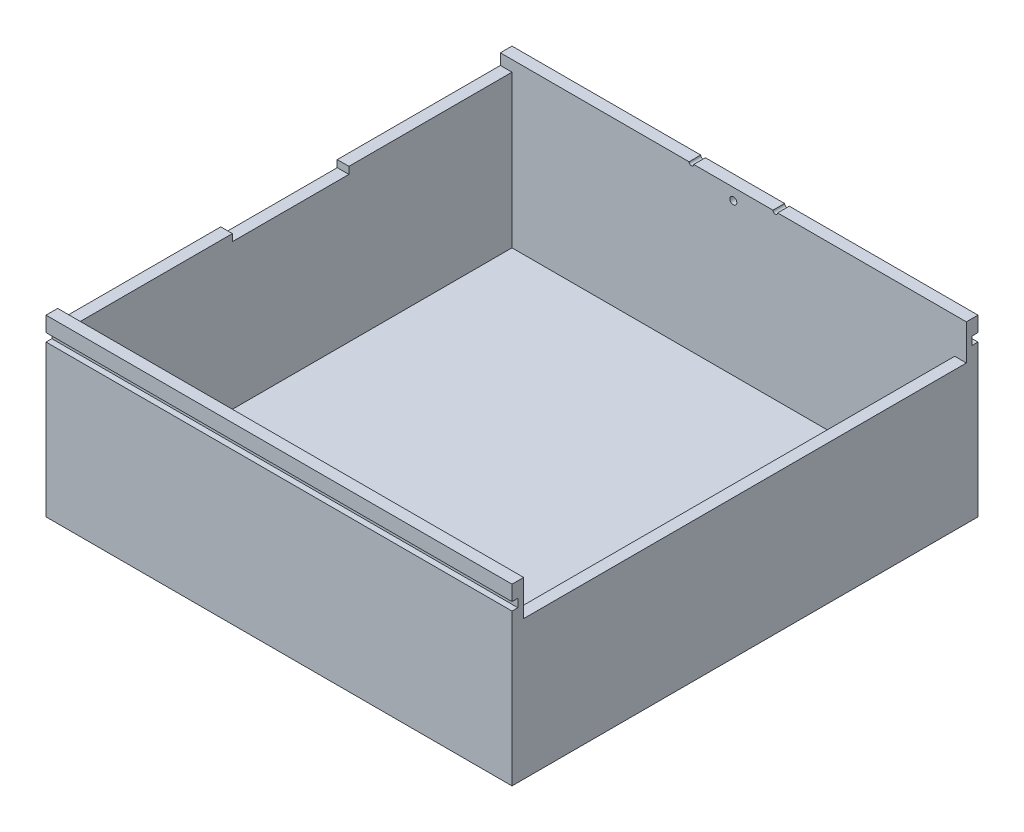
SolidWorks part; units mm, degrees
ref_plane "Спереди" through (0, 0, 0) normal (0, 0, 1) x (1, 0, 0)
ref_plane "Сверху" through (0, 0, 0) normal (0, 1, 0) x (1, 0, 0)
ref_plane "Справа" through (0, 0, 0) normal (1, 0, 0) x (0, 0, -1)
sketch "Эскиз1" plane through (0, 0, 0) normal (0, 1, 0) x (1, 0, 0)
  line L1 (100, -100) -> (-100, -100)
  line L2 (100, -100) -> (100, 100)
  line L3 (100, 100) -> (-100, 100)
  line L4 (-100, -100) -> (-100, 100)
  line L5 (100, -100) -> (-100, 100) construction
  line L6 (100, 100) -> (-100, -100) construction
  point P0 (0, 0)
  dimension "D1" = 200
  dimension "D2" = 200
extrude "Бобышка-Вытянуть2" add sketch "Эскиз1" along normal blind 5
sketch "Эскиз2" plane through (0, 5, 0) normal (0, 1, 0) x (1, 0, 0)
  line L0 (100, -100) -> (100, 100) construction
  line L1 (-100, -100) -> (100, -100)
  line L2 (-100, -100) -> (-100, -95)
  line L3 (-100, -95) -> (100, -95)
  line L4 (100, -100) -> (100, -95)
  point P7 (100, -97.5)
  dimension "D1" = 2.5
extrude "Бобышка-Вытянуть3" add sketch "Эскиз2" along normal blind 70
sketch "Эскиз3" plane through (0, 5, 0) normal (0, 1, 0) x (1, 0, 0)
  line L2 (100, -95) -> (95, -95)
  line L3 (100, -95) -> (100, 95)
  line L4 (100, 95) -> (95, 95)
  line L5 (95, -95) -> (95, 95)
  dimension "D1" = 190
  dimension "D2" = 5
extrude "Бобышка-Вытянуть4" add sketch "Эскиз3" along normal blind 54.7
sketch "Эскиз4" plane through (0, 5, 0) normal (0, 1, 0) x (1, 0, 0)
  line L2 (100, 95) -> (-100, 95)
  line L3 (100, 95) -> (100, 100)
  line L4 (100, 100) -> (-100, 100)
  line L5 (-100, 95) -> (-100, 100)
  dimension "D1" = 5
extrude "Бобышка-Вытянуть5" add sketch "Эскиз4" along normal blind 70
sketch "Эскиз14" plane through (0, 5, 0) normal (0, 1, 0) x (1, 0, 0)
  line L1 (-100, -95) -> (-95, -95)
  line L2 (-100, -95) -> (-100, 95)
  line L3 (-100, 95) -> (-95, 95)
  line L4 (-95, -95) -> (-95, 95)
  dimension "D1" = 5
extrude "Бобышка-Вытянуть7" add sketch "Эскиз14" along normal blind 65.3
sketch "Эскиз15" plane through (0, 70.3, 0) normal (0, 1, 0) x (1, 0, 0)
  line L0 (-95, -95) -> (-95, 95) construction
  line L1 (-95, 0) -> (-100, 0) construction
  line L2 (-100, 95) -> (-100, -95) construction
  line L4 (-100, -25) -> (-95, -25)
  line L5 (-100, -25) -> (-100, 25)
  line L6 (-100, 25) -> (-95, 25)
  line L7 (-95, -25) -> (-95, 25)
  line L8 (-100, -25) -> (-95, 25) construction
  line L9 (-100, 25) -> (-95, -25) construction
  point P6 (-97.5, 0)
  dimension "D1" = 50
extrude "Вырез-Вытянуть7" cut sketch "Эскиз15" against normal blind 3
sketch "Эскиз16" plane through (0, 0, -100) normal (0, 0, -1) x (-1, 0, 0)
  line L0 (-100, 75) -> (100, 75) construction
  line L1 (0, 75) -> (-18, 75) construction
  arc A0 (-19, 75) -> (-17, 75) centre (-18, 75) ccw
  dimension "D1" = 18
  dimension "D3" = 1
extrude "Вырез-Вытянуть8" cut sketch "Эскиз16" against normal blind 5 and the other way through all
sketch "Эскиз18" plane through (0, 0, -100) normal (0, 0, -1) x (-1, 0, 0)
  line L0 (-17, 75) -> (18, 75) construction
  line L1 (-17, 75) -> (100, 75) construction
  arc A0 (17, 75) -> (19, 75) centre (18, 75) ccw
  dimension "D1" = 35
  dimension "D2" = 1
extrude "Вырез-Вытянуть9" cut sketch "Эскиз18" against normal blind 5 and the other way through all
sketch "Эскиз19" plane through (0, 0, -100) normal (0, 0, -1) x (-1, 0, 0)
  line L0 (0, 75) -> (0, 70) construction
  line L1 (-17, 75) -> (17, 75) construction
  circle A0 centre (0, 70) radius 1.5
  dimension "D2" = 3
  dimension "D1" = 5
extrude "Вырез-Вытянуть10" cut sketch "Эскиз19" against normal blind 5
sketch "Эскиз20" plane through (0, 0, 100) normal (0, 0, 1) x (1, 0, 0)
  line L0 (100, 75) -> (100, 68.5) construction
  line L1 (100, 75) -> (100, 0) construction
  line L2 (100, 68.5) -> (80, 68.5) construction
  line L3 (80, 68.5) -> (40, 68.5) construction
  line L4 (40, 68.5) -> (0, 68.5) construction
  line L5 (0, 68.5) -> (-40, 68.5) construction
  line L6 (-40, 68.5) -> (-80, 68.5) construction
  line L7 (-80, 68.5) -> (-100, 68.5) construction
  line L8 (-100, 75) -> (-100, 0) construction
  line L10 (100, 68.5) -> (-100, 68.5)
  line L11 (100, 68.5) -> (100, 65)
  line L12 (100, 65) -> (-100, 65)
  line L13 (-100, 68.5) -> (-100, 65)
  dimension "D1" = 6.5
  dimension "D2" = 20
  dimension "D3" = 40
  dimension "D4" = 40
  dimension "D5" = 40
  dimension "D6" = 40
  dimension "D7" = 20
  dimension "D8" = 3.5
extrude "Вырез-Вытянуть11" cut sketch "Эскиз20" against normal blind 2.5
sketch "Эскиз21" plane through (0, 0, -100) normal (0, 0, -1) x (-1, 0, 0)
  line L0 (-100, 75) -> (-100, 68.5) construction
  line L1 (-100, 75) -> (-100, 0) construction
  line L2 (-18, 74) -> (-18, 55.743) construction
  line L3 (18, 74) -> (18, 62.9105) construction
  line L4 (-100, 68.5) -> (-18, 68.5)
  line L5 (-100, 68.5) -> (-100, 65)
  line L6 (-100, 65) -> (-18, 65)
  line L7 (-18, 68.5) -> (-18, 65)
  line L8 (100, 75) -> (100, 68.5) construction
  line L9 (100, 75) -> (100, 0) construction
  line L11 (100, 68.5) -> (18, 68.5)
  line L12 (100, 68.5) -> (100, 65)
  line L13 (100, 65) -> (18, 65)
  line L14 (18, 68.5) -> (18, 65)
  arc A0 (-19, 75) -> (-17, 75) centre (-18, 75) ccw construction
  arc A1 (17, 75) -> (19, 75) centre (18, 75) ccw construction
  dimension "D1" = 6.5
  dimension "D2" = 3.5
  dimension "D3" = 6.5
  dimension "D4" = 3.5
extrude "Вырез-Вытянуть13" cut sketch "Эскиз21" against normal blind 2.5
